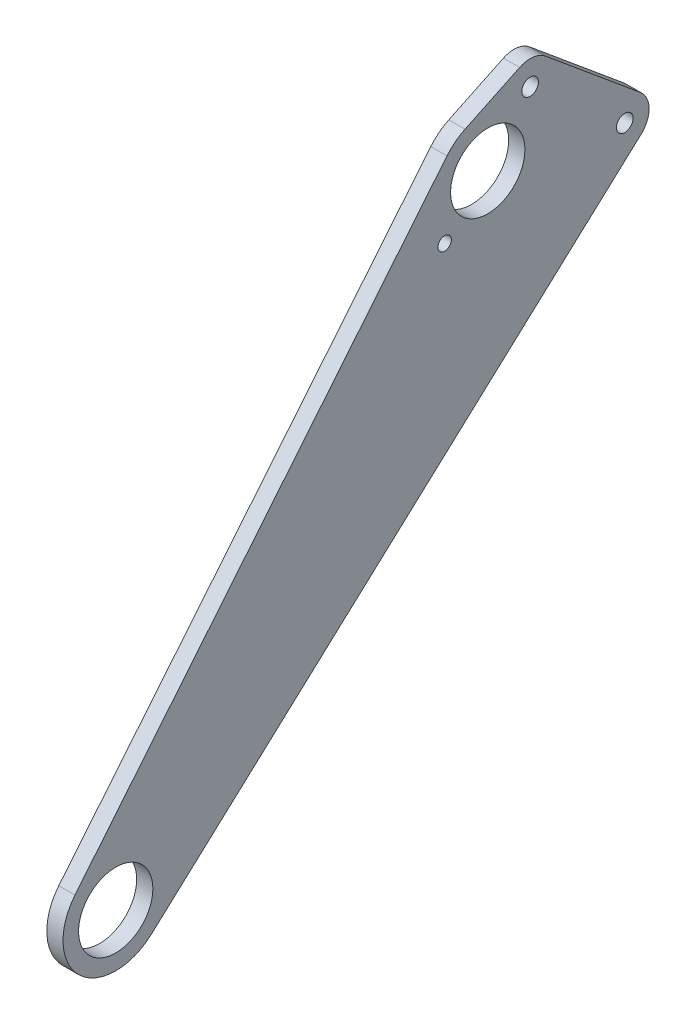
SolidWorks part; units mm, degrees
material "6061-T6 (SS)"
ref_plane "Front Plane" through (0, 0, 0) normal (0, 0, 1) x (1, 0, 0)
ref_plane "Top Plane" through (0, 0, 0) normal (0, 1, 0) x (1, 0, 0)
ref_plane "Right Plane" through (0, 0, 0) normal (1, 0, 0) x (0, 0, -1)
sketch "Sketch1" plane through (0, 0, 0) normal (1, 0, 0) x (0, 0, -1)
  line L0 (0, 0) -> (47.4141, 0) construction
  line L1 (0, 0) -> (143.6841, 143.6841) construction
  line L2 (143.6841, 143.6841) -> (145.7609, 177.9111) construction
  line L3 (0, 0) -> (145.7609, 177.9111) construction
  line L4 (0, 0) -> (199.4397, 167.3498) construction
  line L5 (145.7609, 177.9111) -> (162.3612, 198.173) construction
  line L6 (-15.9639, 13.079) -> (129.797, 190.9902)
  line L7 (136.8535, 196.5274) -> (158.2501, 206.7651)
  line L8 (168.4502, 205.4976) -> (205.5286, 174.6744)
  line L9 (205.8681, 160.3212) -> (13.9282, -15.2286)
  line L10 (144.7225, 160.7976) -> (128.8766, 161.7591) construction
  circle A0 centre (0, 0) radius 14.5542
  circle A1 centre (143.6841, 143.6841) radius 14.5542 construction
  circle A2 centre (145.7609, 177.9111) radius 14.5542
  circle A3 centre (199.4397, 167.3498) radius 3.2639
  circle A4 centre (162.3612, 198.173) radius 3.2639
  arc A5 (168.4502, 205.4976) -> (158.2501, 206.7651) centre (162.3612, 198.173) ccw
  arc A6 (205.8681, 160.3212) -> (205.5286, 174.6744) centre (199.4397, 167.3498) ccw
  arc A7 (136.8535, 196.5274) -> (129.797, 190.9902) centre (145.7609, 177.9111) ccw
  arc A8 (13.9282, -15.2286) -> (-15.9639, 13.079) centre (0, 0) cw
  circle A9 centre (128.8766, 161.7591) radius 2.6289
  dimension "D1" = 29.1084
  dimension "D4" = 34.29
  dimension "D5" = 29.1084
  dimension "D6" = 29.1084
  dimension "D10" = 6.5278
  dimension "D12" = 6.5278
  dimension "D13" = 9.525
  dimension "D14" = 9.525
  dimension "D15" = 20.6375
  dimension "D16" = 20.6375
  dimension "D18" = 5.2578
  dimension "D2" = 45
  dimension "D3" = 203.2
  dimension "D7" = 229.997
  dimension "D8" = 260.35
  dimension "D9" = 40
  dimension "D11" = 26.1937
  dimension "D17" = 15.875
extrude "Boss-Extrude1" add sketch "Sketch1" along normal blind 6.35
sketch3d "3DSketch1"
  point P0 (3.175, 93.26, 20.6375)
